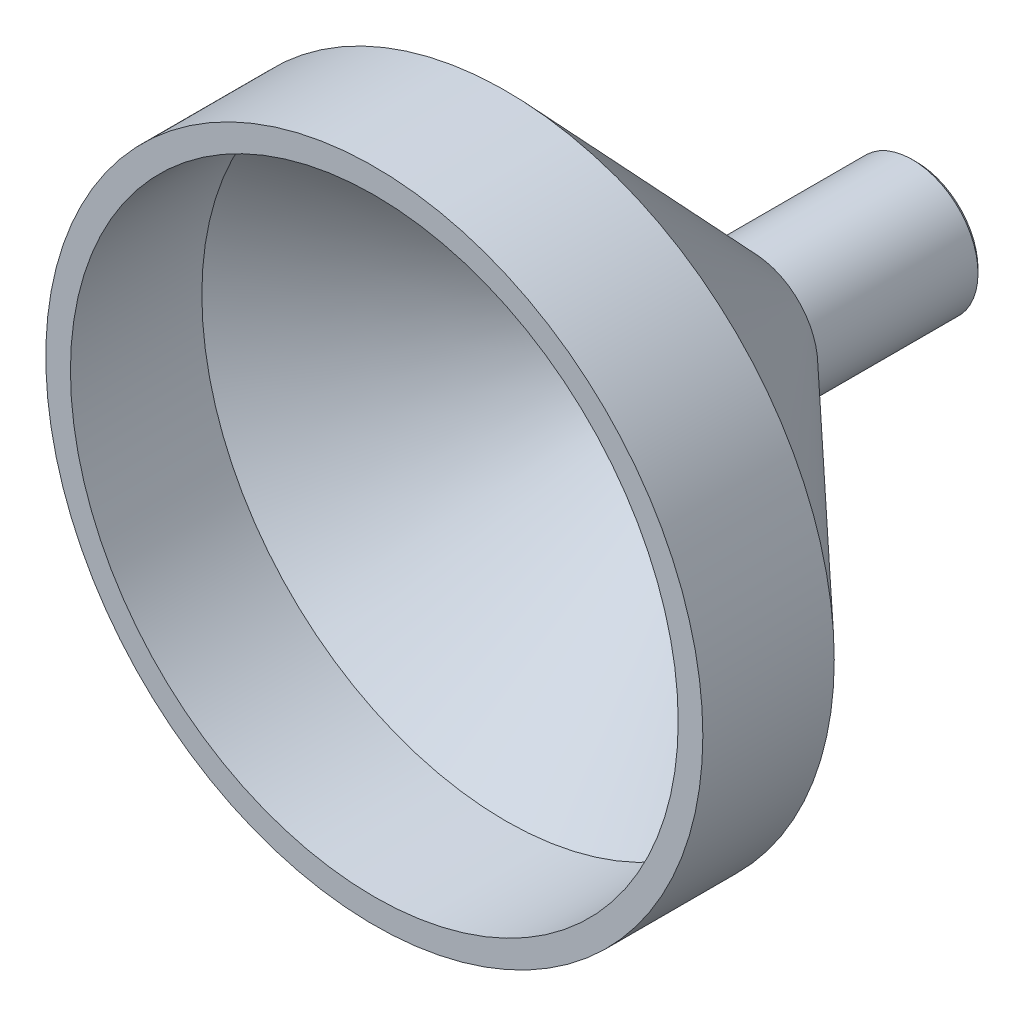
SolidWorks part; units mm, degrees
ref_plane "Front Plane" through (0, 0, 0) normal (0, 0, 1) x (1, 0, 0)
ref_plane "Top Plane" through (0, 0, 0) normal (0, 1, 0) x (1, 0, 0)
ref_plane "Right Plane" through (0, 0, 0) normal (1, 0, 0) x (0, 0, -1)
sketch "Sketch1" plane through (0, 0, 0) normal (0, 1, 0) x (1, 0, 0)
  line L0 (0, 0) -> (0, 25) construction
  line L1 (0, 25) -> (-4, 25) construction
  line L2 (-4, 25) -> (-4, 15)
  line L3 (0, 0) -> (-20, 0) construction
  line L4 (-4, 15) -> (-20, 0)
  line L6 (-4, 25) -> (-3.25, 25)
  line L7 (-18.5, 0) -> (-3.25, 14.2969)
  line L8 (-3.25, 14.2969) -> (-3.25, 25)
  line L9 (-18.5, 0) -> (-18.5, -8)
  line L10 (-18.5, -8) -> (-20, -8)
  line L11 (-20, -8) -> (-20, 0)
  dimension "D1" = 4
  dimension "D2" = 25
  dimension "D3" = 10
  dimension "D4" = 0.75
  dimension "D5" = 1.5
  dimension "D6" = 18.5
  dimension "D7" = 8
revolve "Revolve1" add sketch "Sketch1" angle 360 about L0
chamfer "Chamfer2" distance 0.25 angle 45 1 edges at (4, 0, -25)
